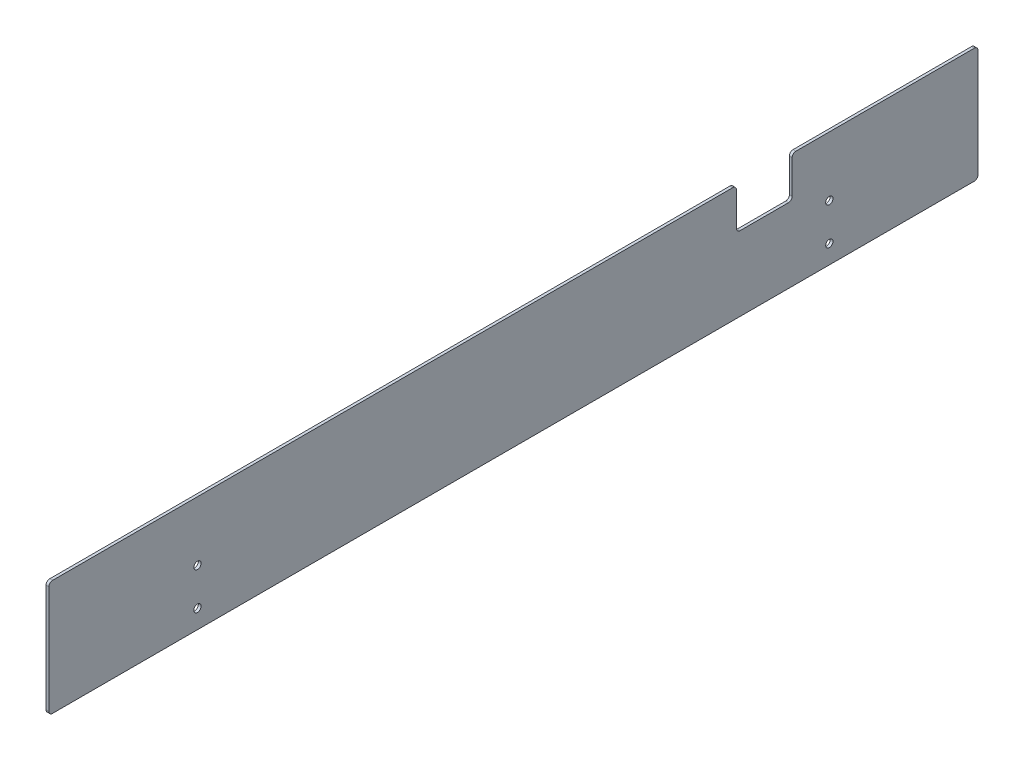
SolidWorks part; units mm, degrees
ref_plane "Front Plane" through (0, 0, 0) normal (0, 0, 1) x (1, 0, 0)
ref_plane "Top Plane" through (0, 0, 0) normal (0, 1, 0) x (1, 0, 0)
ref_plane "Right Plane" through (0, 0, 0) normal (1, 0, 0) x (0, 0, -1)
sketch "Sketch1" plane through (0, 0, 0) normal (1, 0, 0) x (0, 0, -1)
  line L0 (130.0532, -78.2926) -> (230.0532, -78.2926)
  line L1 (-269.9468, -78.2926) -> (100.0532, -78.2926)
  line L2 (-269.9468, -78.2926) -> (-269.9468, -140.2926)
  line L3 (-269.9468, -140.2926) -> (230.0532, -140.2926)
  line L4 (230.0532, -78.2926) -> (230.0532, -140.2926)
  line L6 (130.0532, -78.2926) -> (130.0532, -100.2926)
  line L7 (130.0532, -100.2926) -> (100.0532, -100.2926)
  line L8 (100.0532, -78.2926) -> (100.0532, -100.2926)
  dimension "D1" = 500
  dimension "D2" = 62
  dimension "D3" = 30
  dimension "D4" = 100
  dimension "D5" = 22
extrude "Boss-Extrude1" add sketch "Sketch1" along normal blind 1.5
fillet "Fillet1" radius 2 8 edges at (0.75, -140.2926, -230.0532) (0.75, -140.2926, 269.9468) (0.75, -78.2926, 269.9468) (0.75, -78.2926, -100.0532) (0.75, -100.2926, -100.0532) (0.75, -100.2926, -130.0532) (0.75, -78.2926, -130.0532) (0.75, -78.2926, -230.0532)
sketch "Sketch2" plane through (0, 0, 0) normal (-1, 0, 0) x (0, 0, 1)
  line L0 (-230.0532, -138.2926) -> (-230.0532, -80.2926) construction
  line L1 (267.9468, -140.2926) -> (-228.0532, -140.2926) construction
  line L2 (269.9468, -80.2926) -> (269.9468, -138.2926) construction
  circle A0 centre (-150.0532, -110.2926) radius 1.95
  circle A1 centre (-150.0532, -130.2926) radius 1.95
  circle A2 centre (189.9468, -110.2926) radius 1.95
  circle A3 centre (189.9468, -130.2926) radius 1.95
  dimension "D1" = 80
  dimension "D2" = 20
  dimension "D3" = 10
  dimension "D4" = 80
  dimension "D5" = 20
  dimension "D6" = 10
extrude "Cut-Extrude1" cut sketch "Sketch2" against normal blind 10
